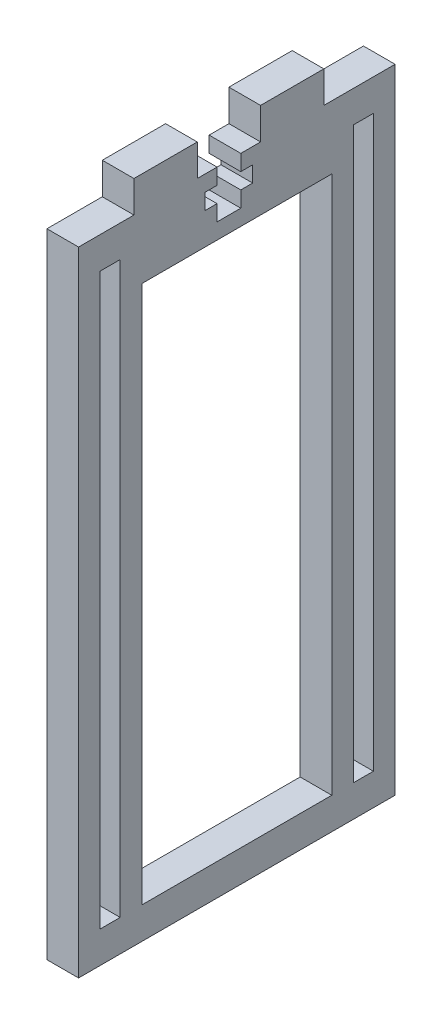
SolidWorks part; units mm, degrees
ref_plane "Front Plane" through (0, 0, 0) normal (0, 0, 1) x (1, 0, 0)
ref_plane "Top Plane" through (0, 0, 0) normal (0, 1, 0) x (1, 0, 0)
ref_plane "Right Plane" through (0, 0, 0) normal (1, 0, 0) x (0, 0, -1)
sketch "Sketch2" plane through (0, 0, 0) normal (1, 0, 0) x (0, 0, -1)
  line L0 (6.35, 120.65) -> (6.35, 84.4561)
  line L1 (0, 0) -> (63.5, 0)
  line L2 (0, 0) -> (0, 127) construction
  line L3 (0, 127) -> (11.1125, 127)
  line L4 (63.5, 0) -> (63.5, 127) construction
  line L5 (12.7, 0) -> (50.8, 0)
  line L6 (12.7, 0) -> (12.7, 114.3) construction
  line L7 (12.7, 114.3) -> (50.8, 114.3)
  line L8 (50.8, 0) -> (50.8, 114.3) construction
  line L9 (0, 0) -> (-3.175, 0)
  line L10 (0, 0) -> (0, 127) construction
  line L11 (49.2125, 127) -> (63.5, 127)
  line L12 (23.8125, 127) -> (36.5125, 127)
  line L13 (12.7, 0) -> (15.875, 0)
  line L14 (12.7, 0) -> (12.7, 114.3) construction
  line L15 (12.7, 114.3) -> (15.875, 114.3)
  line L16 (59.15, 114.3) -> (55.15, 114.3)
  line L17 (79.375, 114.3) -> (63.5, 114.3)
  line L19 (79.375, 0) -> (50.8, 0)
  line L20 (50.8, 114.3) -> (50.8, 0) construction
  line L22 (63.5, 0) -> (63.5, 127) construction
  line L25 (4.35, 120.65) -> (8.35, 120.65)
  line L26 (4.35, 120.65) -> (4.35, 6.35)
  line L27 (4.35, 6.35) -> (8.35, 6.35)
  line L28 (8.35, 120.65) -> (8.35, 6.35)
  line L29 (55.15, 120.65) -> (59.15, 120.65)
  line L30 (55.15, 120.65) -> (55.15, 6.35)
  line L31 (55.15, 6.35) -> (59.15, 6.35)
  line L32 (59.15, 120.65) -> (59.15, 6.35)
  line L33 (57.15, 120.65) -> (57.15, 86.4127)
  line L34 (0, 127) -> (0, 0)
  line L36 (11.1125, 127) -> (11.1125, 133.35)
  line L37 (11.1125, 133.35) -> (23.8125, 133.35)
  line L38 (23.8125, 127) -> (23.8125, 133.35)
  line L40 (36.5125, 127) -> (36.5125, 133.35)
  line L41 (36.5125, 133.35) -> (49.2125, 133.35)
  line L42 (49.2125, 127) -> (49.2125, 133.35)
  line L43 (12.7, 0) -> (12.7, 114.3)
  line L44 (50.8, 114.3) -> (50.8, 0)
  line L45 (63.5, 0) -> (63.5, 127)
  dimension "D1" = 63.5
  dimension "D2" = 127
  dimension "D3" = 12.7
  dimension "D4" = 12.7
  dimension "D9" = 114.3
  dimension "D10" = 6.35
  dimension "D11" = 6.35
  dimension "D12" = 4
  dimension "D13" = 4
  dimension "D14" = 50.8
  dimension "D16" = 6.35
  dimension "D17" = 6.35
  dimension "D18" = 6.35
  dimension "D19" = 12.7
  dimension "D20" = 6.35
  dimension "D21" = 12.7
  dimension "D22" = 12.7
  dimension "D23" = 4.7625
extrude "Boss-Extrude1" add sketch "Sketch2" along normal blind 6.35 contours L1 L45 L11 L42 L41 L40 L12 L38 L37 L36 L3 L34 L43 L7 L44 L29 L32 L31 L30 L25 L28 L27 L26
sketch "Sketch4" plane through (0, 0, 0) normal (-1, 0, 0) x (0, 0, 1)
  line L0 (-23.8125, 127) -> (-36.5125, 127) construction
  line L1 (-27.7812, 127) -> (-32.5437, 127)
  line L2 (-27.7812, 127) -> (-27.7812, 117.475)
  line L3 (-27.7812, 117.475) -> (-32.5438, 117.475)
  line L4 (-32.5437, 127) -> (-32.5438, 117.475)
  line L5 (-23.8125, 127) -> (-23.8125, 133.35) construction
  line L6 (-34.925, 120.65) -> (-25.4, 120.65)
  line L7 (-34.925, 120.65) -> (-34.925, 123.825)
  line L8 (-34.925, 123.825) -> (-25.4, 123.825)
  line L9 (-25.4, 120.65) -> (-25.4, 123.825)
  point P10 (-23.8125, 130.175)
  dimension "D1" = 9.525
  dimension "D2" = 3.175
  dimension "D3" = 3.175
  dimension "D4" = 9.525
  dimension "D5" = 2.3813
  dimension "D6" = 4.7625
  dimension "D7" = 3.9688
extrude "Cut-Extrude1" cut sketch "Sketch4" against normal blind 6.35 contours L2 L3 L4 L1 | L6 L9 L8 L7
sketch "Sketch6" plane through (6.35, 0, 0) normal (1, 0, 0) x (0, 0, -1)
  line L0 (50.8, 114.3) -> (50.8, 0) construction
  line L1 (12.7, 0) -> (50.8, 0)
  line L2 (12.7, 0) -> (12.7, 6.35)
  line L3 (12.7, 6.35) -> (50.8, 6.35)
  line L4 (50.8, 0) -> (50.8, 6.35)
extrude "Boss-Extrude3" add sketch "Sketch6" against normal blind 6.35
